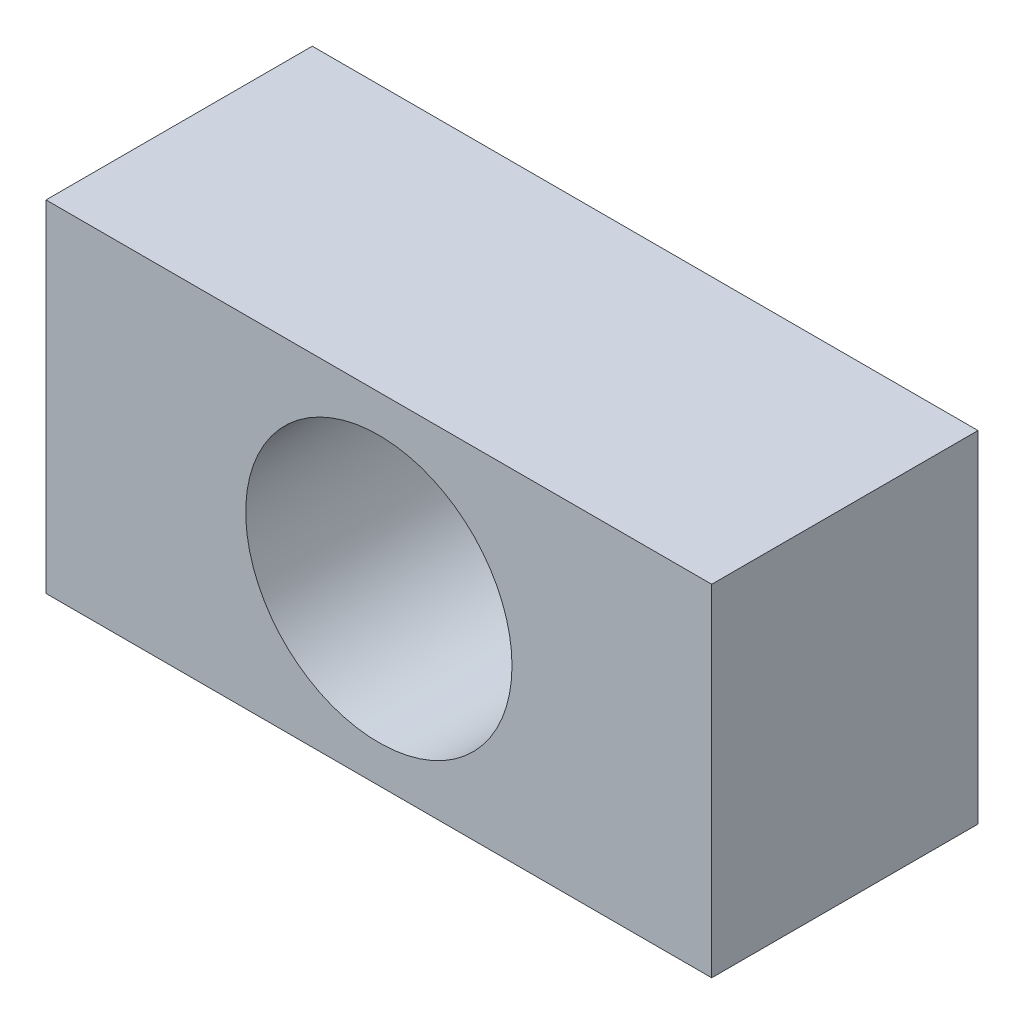
SolidWorks part; units mm, degrees
ref_plane "前视基准面" through (0, 0, 0) normal (0, 0, 1) x (1, 0, 0)
ref_plane "上视基准面" through (0, 0, 0) normal (0, 1, 0) x (1, 0, 0)
ref_plane "右视基准面" through (0, 0, 0) normal (1, 0, 0) x (0, 0, -1)
sketch "草图1" plane through (0, 0, 0) normal (0, 0, 1) x (1, 0, 0)
  line L1 (-2.6591, 0.0559) -> (4.8409, 0.0559)
  line L2 (-2.6591, 0.0559) -> (-2.6591, -3.7841)
  line L3 (-2.6591, -3.7841) -> (4.8409, -3.7841)
  line L4 (4.8409, 0.0559) -> (4.8409, -3.7841)
  circle A0 centre (1.0909, -1.8641) radius 1.5
  dimension "D1" = 7.5
  dimension "D2" = 3.84
extrude "凸台-拉伸1" add sketch "草图1" along normal blind 3
